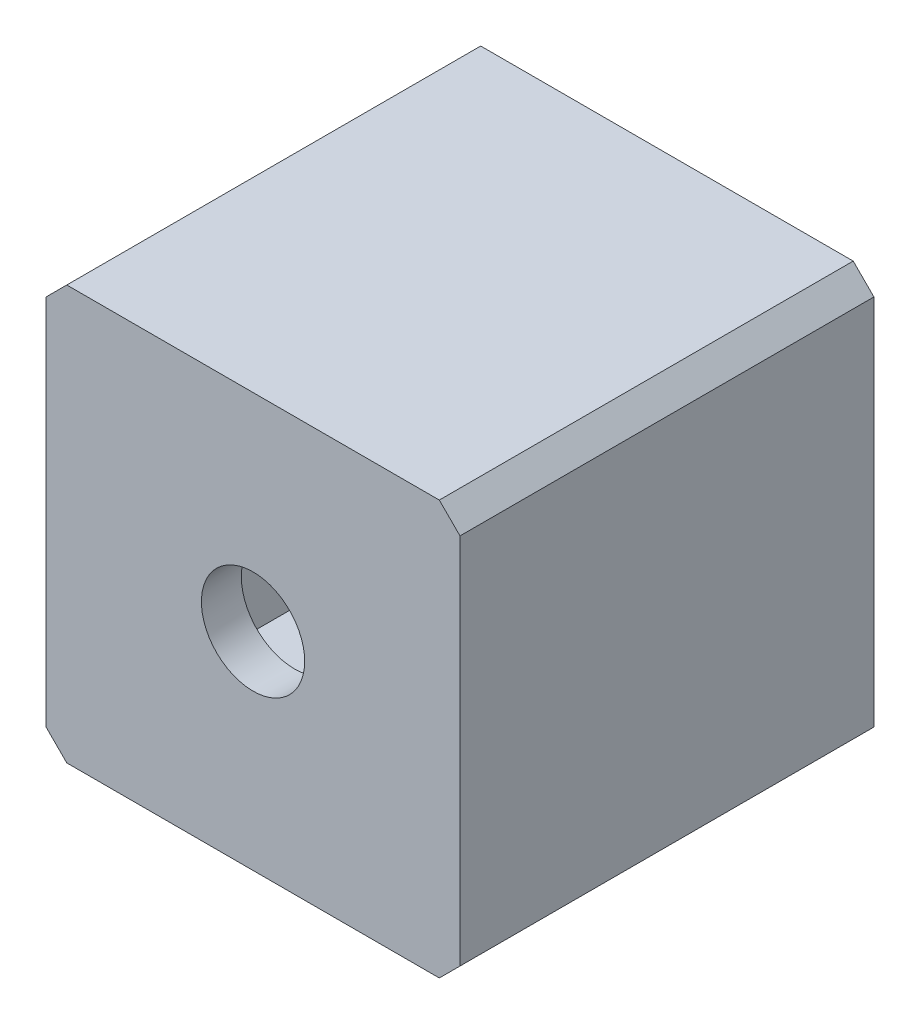
SolidWorks part; units mm, degrees
ref_plane "Plan de face" through (0, 0, 0) normal (0, 0, 1) x (1, 0, 0)
ref_plane "Plan de dessus" through (0, 0, 0) normal (0, 1, 0) x (1, 0, 0)
ref_plane "Plan de droite" through (0, 0, 0) normal (1, 0, 0) x (0, 0, -1)
sketch "Esquisse1" plane through (0, 0, 0) normal (0, 0, 1) x (1, 0, 0)
  line L1 (-34.6304, 29.1827) -> (-14.6304, 29.1827)
  line L2 (-34.6304, 29.1827) -> (-34.6304, 9.1827)
  line L3 (-34.6304, 9.1827) -> (-14.6304, 9.1827)
  line L4 (-14.6304, 29.1827) -> (-14.6304, 9.1827)
  dimension "D1" = 20
  dimension "21" = 20
extrude "Boss.-Extru.1" add sketch "Esquisse1" along normal blind 20
sketch "Esquisse2" plane through (0, 0, 20) normal (0, 0, 1) x (1, 0, 0)
  line L0 (-24.6304, 29.1827) -> (-24.6304, 9.1827) construction
  line L1 (-14.6304, 29.1827) -> (-34.6304, 29.1827) construction
  line L2 (-34.6304, 9.1827) -> (-14.6304, 9.1827) construction
  line L3 (-34.6304, 19.1827) -> (-14.6304, 19.1827) construction
  line L4 (-34.6304, 29.1827) -> (-34.6304, 9.1827) construction
  line L5 (-14.6304, 9.1827) -> (-14.6304, 29.1827) construction
  circle A0 centre (-24.6304, 19.1827) radius 2.6
  dimension "D1" = 5.2
extrude "Enlèv. mat.-Extru.1" cut sketch "Esquisse2" along normal through all draft 2 from offset 3 offset against normal yes
sketch "Esquisse3" plane through (0, 0, 0) normal (0, 0, -1) x (-1, 0, 0)
  line L0 (14.6304, 9.1827) -> (14.6304, 29.1827) construction
  line L1 (16.6304, 27.1827) -> (32.6304, 27.1827)
  line L2 (16.6304, 27.1827) -> (16.6304, 11.1827)
  line L3 (16.6304, 11.1827) -> (32.6304, 11.1827)
  line L4 (32.6304, 27.1827) -> (32.6304, 11.1827)
  line L5 (14.6304, 29.1827) -> (34.6304, 29.1827) construction
  line L6 (14.6304, 19.1827) -> (34.6304, 19.1827) construction
  line L7 (34.6304, 29.1827) -> (34.6304, 9.1827) construction
  line L8 (24.6304, 29.1827) -> (24.6304, 9.1827) construction
  line L9 (34.6304, 9.1827) -> (14.6304, 9.1827) construction
  dimension "D1" = 2
  dimension "2" = 2
extrude "Enlèv. mat.-Extru.2" cut sketch "Esquisse3" against normal blind 18
chamfer "Chanfrein1" distance 1 angle 45 4 edges at (-14.6304, 9.1827, 10) (-14.6304, 29.1827, 10) (-34.6304, 29.1827, 10) (-34.6304, 9.1827, 10)
